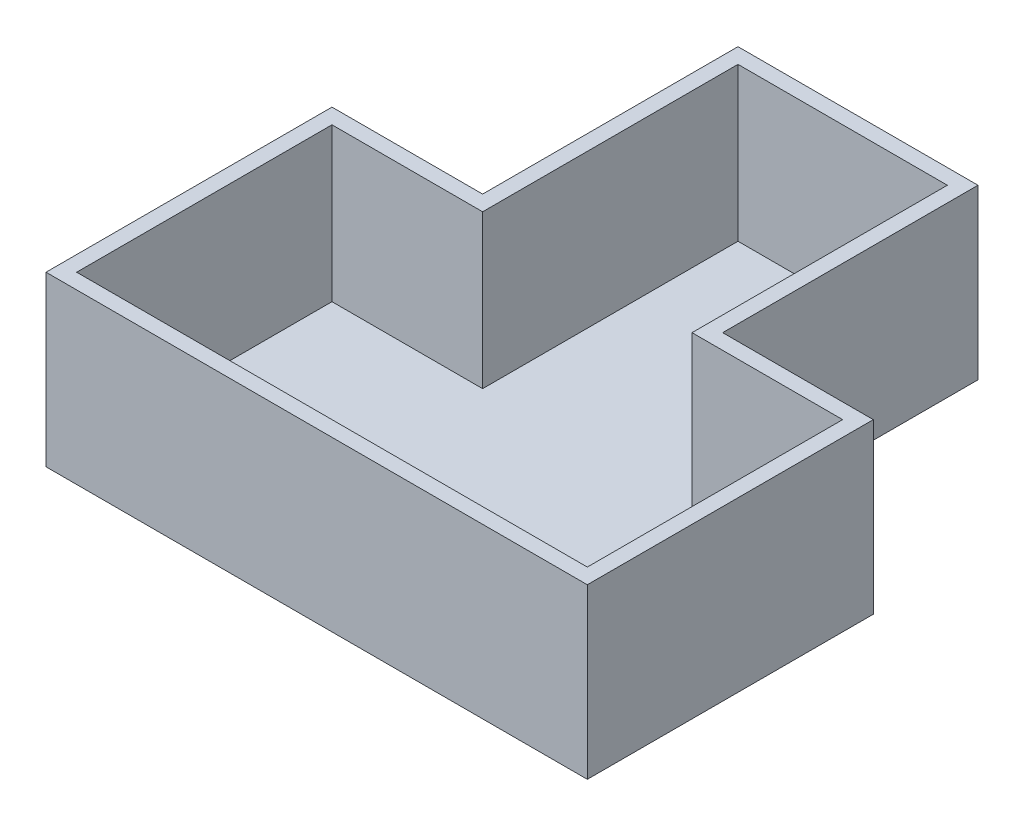
SolidWorks part; units mm, degrees
ref_plane "Front Plane" through (0, 0, 0) normal (0, 0, 1) x (1, 0, 0)
ref_plane "Top Plane" through (0, 0, 0) normal (0, 1, 0) x (1, 0, 0)
ref_plane "Right Plane" through (0, 0, 0) normal (1, 0, 0) x (0, 0, -1)
sketch "Sketch1" plane through (0, 0, 0) normal (0, 1, 0) x (1, 0, 0)
  line L0 (0, 48.994) -> (0, -51.006) construction
  line L5 (20.5, 48.994) -> (-20.5, 48.994)
  line L6 (-20.5, 48.994) -> (-20.5, -1.006)
  line L7 (-20.5, -1.006) -> (-50, -1.006)
  line L8 (-50, -1.006) -> (-50, -51.006)
  line L9 (-50, -51.006) -> (50, -51.006)
  line L10 (50, -1.006) -> (50, -51.006)
  line L11 (20.5, -1.006) -> (50, -1.006)
  line L12 (20.5, 48.994) -> (20.5, -1.006)
  dimension "D1" = 41
  dimension "D2" = 50
  dimension "D3" = 100
  dimension "D4" = 50
extrude "Boss-Extrude1" add sketch "Sketch1" along normal blind 30
shell "Shell1" thickness 3
ref_plane "Plane1" through (0, 10, 0) normal (0, 1, 0) x (1, 0, 0)
